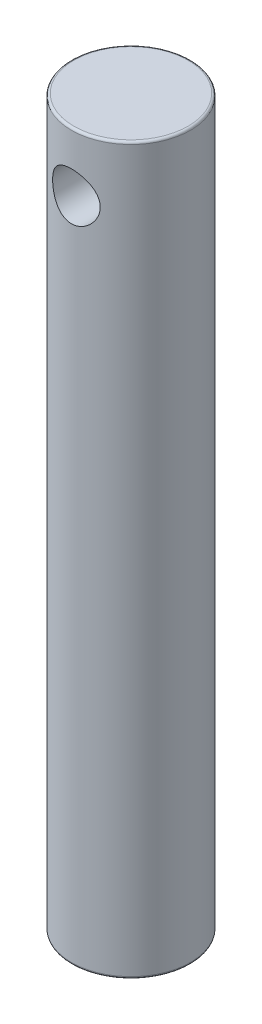
SolidWorks part; units mm, degrees
ref_plane "Front Plane" through (0, 0, 0) normal (0, 0, 1) x (1, 0, 0)
ref_plane "Top Plane" through (0, 0, 0) normal (0, 1, 0) x (1, 0, 0)
ref_plane "Right Plane" through (0, 0, 0) normal (1, 0, 0) x (0, 0, -1)
sketch "Sketch1" plane through (0, 0, 0) normal (0, 0, 1) x (1, 0, 0)
  line L0 (0, 0) -> (0, 152.4)
  dimension "D1" = 152.4
sweep "Sweep1" add path "Sketch1" circular profile diameter 25 parameters "D3"=25
sketch "Sketch6" plane through (0, 0, 0) normal (0, 0, 1) x (1, 0, 0)
  line L0 (12.5, 152.4) -> (-12.5, 152.4) construction
  circle A0 centre (0, 139.9) radius 5
  dimension "D2" = 10
  dimension "D1" = 12.5
extrude "Cut-Extrude1" cut sketch "Sketch6" against normal through all both and the other way through all
fillet "Fillet1" radius 0.5 2 edges at (0, 0, 12.5) (0, 152.4, 12.5)
